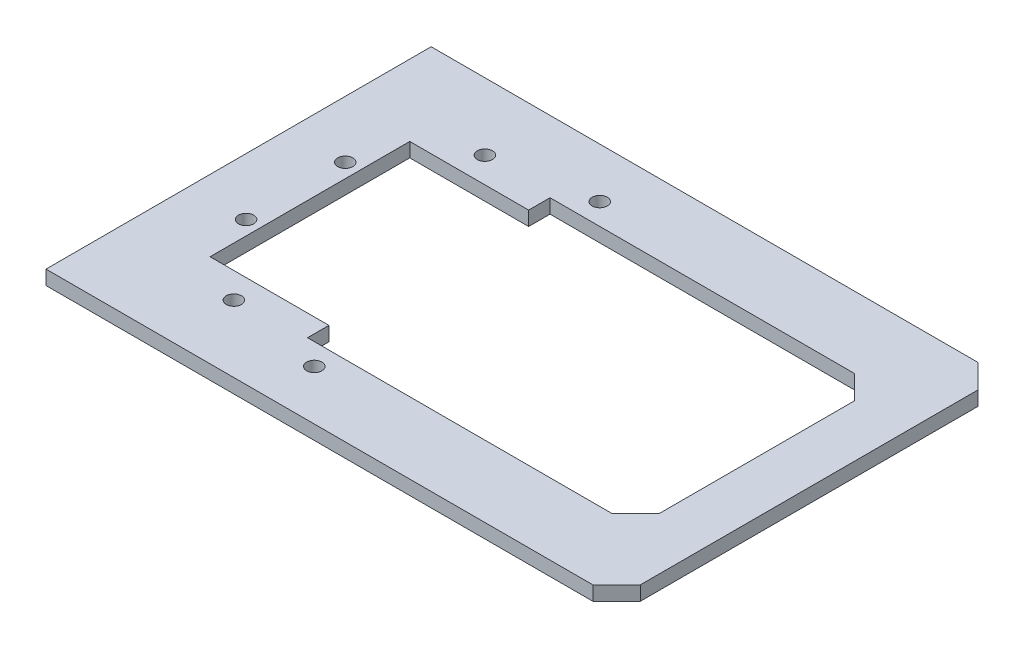
SolidWorks part; units mm, degrees
ref_plane "Front Plane" through (0, 0, 0) normal (0, 0, 1) x (1, 0, 0)
ref_plane "Top Plane" through (0, 0, 0) normal (0, 1, 0) x (1, 0, 0)
ref_plane "Right Plane" through (0, 0, 0) normal (1, 0, 0) x (0, 0, -1)
sketch "Sketch1" plane through (0, 0, 0) normal (0, 1, 0) x (1, 0, 0)
  line L0 (86.5353, -155.1172) -> (97.1189, -155.1172) construction
  line L1 (-18.4647, -134.1172) -> (6.5353, -134.1172)
  line L2 (6.5353, -134.1172) -> (6.5353, -129.6172)
  line L3 (86.5353, -129.6172) -> (86.5353, -119.6172)
  line L4 (81.5353, -114.6172) -> (-33.4647, -114.6172)
  line L5 (-33.4647, -114.6172) -> (-33.4647, -195.6172)
  line L6 (-33.4647, -195.6172) -> (81.5353, -195.6172)
  line L7 (86.5353, -190.6172) -> (86.5353, -180.6172)
  line L8 (6.5353, -129.6172) -> (70.5353, -129.6172)
  line L9 (70.5353, -180.6172) -> (6.5353, -180.6172)
  line L10 (6.5353, -180.6172) -> (6.5353, -176.1172)
  line L11 (6.5353, -176.1172) -> (-18.4647, -176.1172)
  line L12 (-18.4647, -155.1172) -> (-15.8239, -155.1172) construction
  line L13 (86.5353, -129.6172) -> (86.5353, -180.6172)
  line L14 (-18.4647, -134.1172) -> (-18.4647, -176.1172)
  line L15 (86.5353, -119.6172) -> (81.5353, -114.6172)
  line L16 (75.5353, -134.6172) -> (75.5353, -175.6172)
  line L17 (70.5353, -129.6172) -> (75.5353, -134.6172)
  line L18 (81.5353, -195.6172) -> (86.5353, -190.6172)
  line L19 (75.5353, -175.6172) -> (70.5353, -180.6172)
  line L20 (-21.4647, -144.6924) -> (-21.4647, -165.542) construction
  line L21 (-21.4647, -155.1172) -> (-23.3158, -155.1172) construction
  circle A0 centre (12.4699, -125.1003) radius 1.6
  circle A1 centre (-8.0629, -128.7208) radius 1.6
  circle A2 centre (-21.4647, -144.6924) radius 1.6
  circle A3 centre (-21.4647, -165.542) radius 1.6
  circle A4 centre (-8.0629, -181.5137) radius 1.6
  circle A5 centre (12.4699, -185.1342) radius 1.6
  point P6 (75.5353, -129.6172)
  point P7 (75.5353, -180.6172)
  point P26 (86.5353, -114.6172)
  point P29 (86.5353, -195.6172)
  dimension "D13" = 94
  dimension "D14" = 25
  dimension "D19" = 3.2
  dimension "D20" = 3.2
  dimension "D21" = 3.2
  dimension "D22" = 3.2
  dimension "D23" = 3.2
  dimension "D24" = 3.2
  dimension "D2" = 42
  dimension "D3" = 3
  dimension "D4" = 51
  dimension "D5" = 15
  dimension "D6" = 15
  dimension "D7" = 120
  dimension "D8" = 120
  dimension "D9" = 4.5
  dimension "D10" = 80
  dimension "D11" = 80
  dimension "D12" = 81
extrude "Boss-Extrude1" add sketch "Sketch1" along normal blind 3
